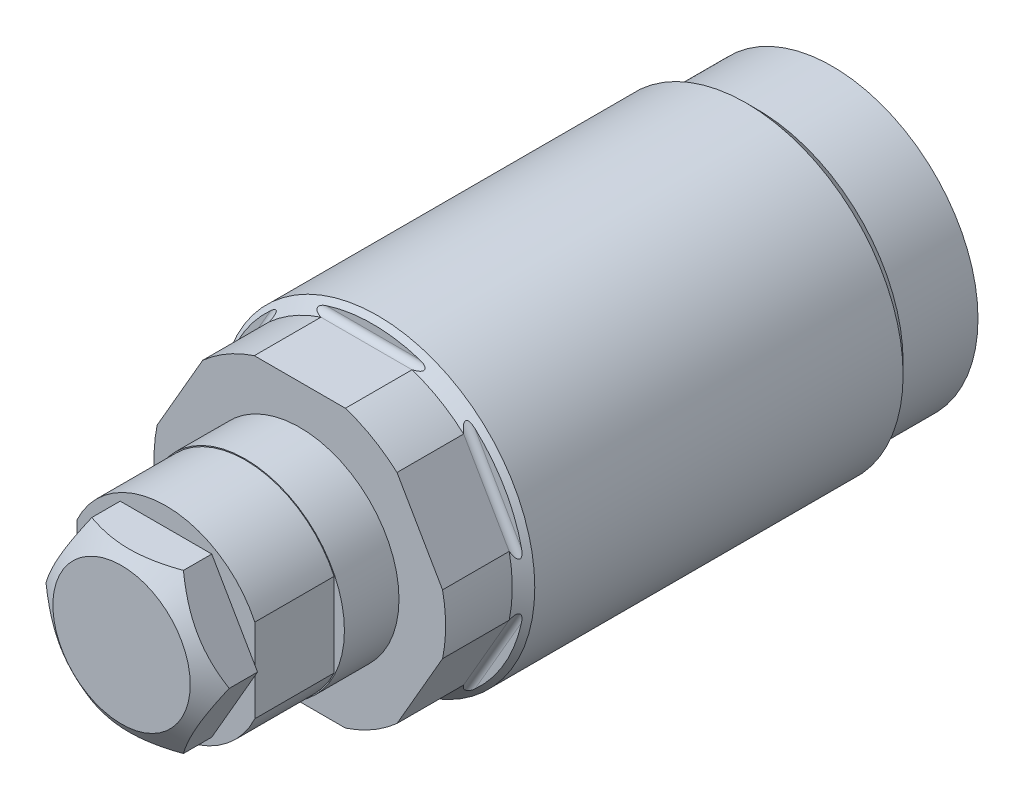
SolidWorks part; units mm, degrees
material "Alloy Steel"
ref_plane "Front Plane" through (0, 0, 0) normal (0, 0, 1) x (1, 0, 0)
ref_plane "Top Plane" through (0, 0, 0) normal (0, 1, 0) x (1, 0, 0)
ref_plane "Right Plane" through (0, 0, 0) normal (1, 0, 0) x (0, 0, -1)
ref_plane "Plane1" through (0, 0, 0) normal (0, 0, 1) x (1, 0, 0)
sketch "Sketch1" plane through (0, 0, 0) normal (0, 0, 1) x (1, 0, 0)
  circle A0 centre (0, 0) radius 12.573
  dimension "D1" = 25.146
extrude "Extrude1" add sketch "Sketch1" along normal blind 42.6212
ref_plane "Plane2" through (0, 0, 0) normal (1, 0, 0) x (0, 0, 1)
sketch "Sketch2" plane through (0, 0, 0) normal (1, 0, 0) x (0, 0, 1)
  line L0 (36.7792, 12.573) -> (36.7792, 11.5951)
  line L1 (37.2872, 11.0871) -> (42.6212, 11.0871)
  line L2 (35.9791, 0) -> (42.4053, 0) construction
  line L3 (42.6212, -12.573) -> (42.6212, 12.573) construction
  line L4 (36.7792, 12.573) -> (42.6212, 12.573)
  line L5 (42.6212, 12.573) -> (42.6212, 11.0871)
  arc A0 (36.7792, 11.5951) -> (37.2872, 11.0871) centre (37.2872, 11.5951) ccw
  dimension "D3" = 0.508
  dimension "D1" = 22.1742
  dimension "D2" = 5.842
extrude "Cut-Extrude1" cut sketch "Sketch2" against normal mid plane 30.1752
ref_plane "Plane12" through (0, 0, 0) normal (1, 0, 0) x (0, 0, -1)
sketch "Sketch10" plane through (0, 0, 0) normal (1, 0, 0) x (0, 0, -1)
  line L0 (-42.6212, 11.6713) -> (-37.2872, 11.6713)
  line L1 (-37.2872, 11.6713) -> (-36.3855, 12.573)
  line L2 (-36.3855, 12.573) -> (-42.6212, 12.573)
  line L3 (-42.6212, 12.573) -> (-42.6212, 11.6713)
  line L4 (-42.425, 0) -> (-35.5657, 0) construction
  line L5 (0, 12.573) -> (-42.6212, 12.573) construction
  line L6 (-42.6212, 12.573) -> (-42.6212, -11.0871) construction
  dimension "D1" = 23.3426
  dimension "D2" = 5.334
  dimension "D3" = 45
revolve "Cut-Revolve1" cut sketch "Sketch10" angle 360 about L4
ref_plane "Plane13" through (0, 0, 0) normal (1, 0, 0) x (0, 0, 1)
sketch "Sketch11" plane through (0, 0, 0) normal (1, 0, 0) x (0, 0, 1)
  line L0 (0, 11.6713) -> (5.9944, 11.6713)
  line L1 (5.9944, 11.6713) -> (6.8961, 12.573)
  line L2 (6.8961, 12.573) -> (0, 12.573)
  line L3 (0, 12.573) -> (0, 11.6713)
  line L4 (-0.3448, 0) -> (7.2409, 0) construction
  line L5 (36.3855, 12.573) -> (0, 12.573) construction
  line L6 (0, 12.573) -> (0, -12.573) construction
  dimension "D1" = 23.3426
  dimension "D2" = 5.9944
  dimension "D3" = 45
revolve "Cut-Revolve2" cut sketch "Sketch11" angle 360 about L4
ref_plane "Plane14" through (0, 0, 0) normal (1, 0, 0) x (0, 0, -1)
sketch "Sketch12" plane through (0, 0, 0) normal (1, 0, 0) x (0, 0, -1)
  line L0 (-42.6212, 0) -> (-53.34, 0)
  line L1 (-53.34, 0) -> (-53.34, 7.9375)
  line L2 (-53.34, 7.9375) -> (-42.6212, 7.9375)
  line L3 (-42.6212, 7.9375) -> (-42.6212, 0)
  line L4 (-53.768, 0) -> (-22.5282, 0) construction
  line L5 (-42.6212, 11.6713) -> (-42.6212, -11.0871) construction
  dimension "D1" = 10.7188
  dimension "D2" = 15.875
revolve "Revolve1" add sketch "Sketch12" angle 360 about L4
ref_plane "Plane15" through (-3.4544, 0, 53.213) normal (0, 1, 0) x (-1, 0, 0)
sketch "S2D0011" plane through (-3.4544, 0, 53.213) normal (0, 1, 0) x (-1, 0, 0)
  line L0 (0, 0.127) -> (0, -4.699)
  line L1 (0, -4.699) -> (-3.4544, -4.699)
  line L2 (0, 0.127) -> (-3.4544, 0.127)
  line L3 (-3.4544, 0.127) -> (-3.4544, -4.699)
  line L4 (-3.4544, -26.196) -> (-3.4544, 0.2413) construction
  line L5 (4.4831, 0.127) -> (-11.3919, 0.127) construction
  dimension "D1" = 4.826
  dimension "D2" = 6.9088
revolve "Cut-Revolve3" cut sketch "S2D0011" angle 360 about L4
ref_plane "Plane16" through (0, 0, 46.863) normal (0, 0, -1) x (0, 1, 0)
ref_plane "Plane17" through (0, 0, 46.863) normal (0, 0, -1) x (0, 1, 0)
sketch "Sketch15" plane through (0, 0, 53.34) normal (0, 0, -1) x (0, 1, 0)
  line L0 (-3.5247, 7.112) -> (3.5247, 7.112)
  line L1 (-3.5247, -7.112) -> (3.5247, -7.112)
  line L2 (-8.7312, 0) -> (8.7312, 0) construction
  arc A0 (3.5247, 7.112) -> (-3.5247, 7.112) centre (0, 0) ccw
  arc A1 (-3.5247, -7.112) -> (3.5247, -7.112) centre (0, 0) ccw
  dimension "D2" = 7.9375
  dimension "D1" = 14.224
extrude "Cut-Extrude10" cut sketch "Sketch15" along normal blind 6.35
sketch "Sketch16" plane through (0, 0, 53.34) normal (0, 0, 1) x (1, 0, 0)
  line L0 (-3.6662, 6.35) -> (3.6662, 6.35)
  line L1 (3.6662, 6.35) -> (7.3323, 0)
  line L2 (7.3323, 0) -> (3.6662, -6.35)
  line L3 (3.6662, -6.35) -> (-3.6662, -6.35)
  line L4 (-3.6662, -6.35) -> (-7.3323, 0)
  line L5 (-7.3323, 0) -> (-3.6662, 6.35)
  line L6 (-8.0656, 0) -> (8.0656, 0) construction
  point P8 (0, 0)
  dimension "D1" = 12.7
  dimension "D2" = 120
  dimension "D3" = 12.7
  dimension "D4" = 6.35
extrude "Extrude2" add sketch "Sketch16" along normal blind 3.556
ref_plane "Plane18" through (0, 0, 0) normal (0, 1, 0) x (1, 0, 0)
sketch "Sketch17" plane through (0, 0, 0) normal (0, 1, 0) x (1, 0, 0)
  line L0 (5.4991, -56.896) -> (7.3323, -55.6123)
  line L1 (0, -56.8332) -> (0, -48.9882) construction
  line L3 (7.3323, -56.896) -> (3.6662, -56.896) construction
  line L4 (7.3323, -55.6123) -> (7.3323, -56.896)
  line L5 (7.3323, -56.896) -> (5.4991, -56.896)
  dimension "D1" = 10.9982
  dimension "D2" = 35
revolve "Cut-Revolve4" cut sketch "Sketch17" angle 360 about L1
pattern_circular "CirPattern2" count 6 over 360 about axis through (0, 0, 0) along (0, 0, 1) of "Cut-Extrude1"
sketch "Sketch18" plane through (0, 0, 0) normal (1, 0, 0) x (0, 0, -1)
  line L0 (0, 0) -> (-56.896, 0) construction
  line L1 (-56.896, 5.4991) -> (-56.896, -5.4991) construction
  line L2 (-53.34, 7.8613) -> (-46.99, 7.8613)
  line L3 (-53.34, 7.9375) -> (-53.34, 3.5247) construction
  line L4 (-46.99, 7.8613) -> (-46.99, 7.9375)
  line L5 (-42.6212, 7.9375) -> (-53.34, 7.9375) construction
  line L6 (-46.99, 7.9375) -> (-53.34, 7.9375)
  line L7 (-53.34, 7.9375) -> (-53.34, 7.8613)
  dimension "D1" = 6.35
  dimension "D2" = 15.7226
revolve "Cut-Revolve5" cut sketch "Sketch18" angle 360 about L0
